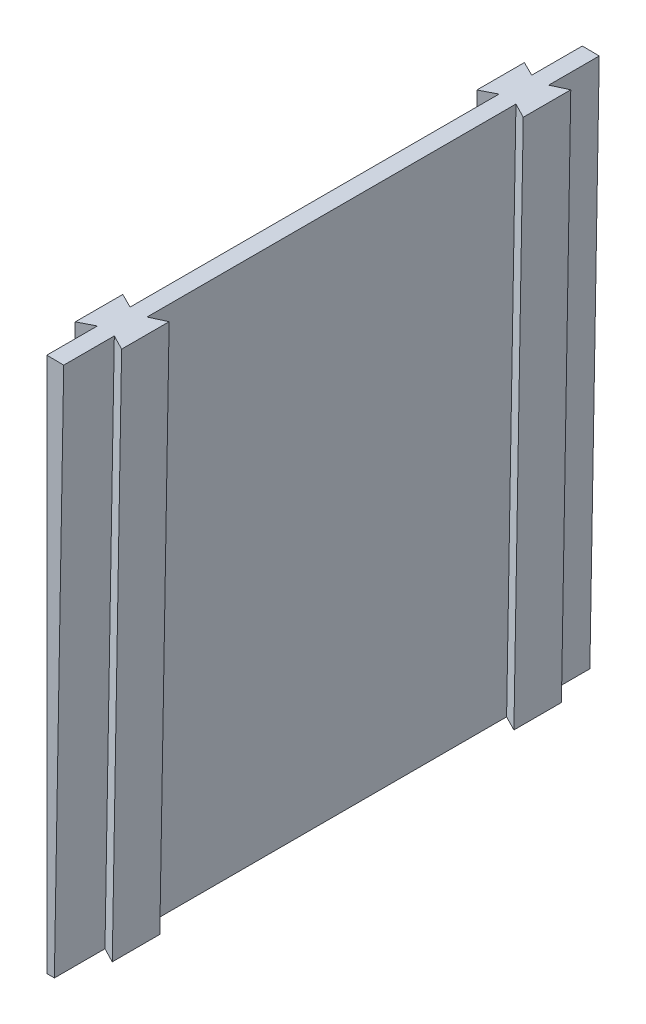
SolidWorks part; units mm, degrees
ref_plane "Front Plane" through (0, 0, 0) normal (0, 0, 1) x (1, 0, 0)
ref_plane "Top Plane" through (0, 0, 0) normal (0, 1, 0) x (1, 0, 0)
ref_plane "Right Plane" through (0, 0, 0) normal (1, 0, 0) x (0, 0, -1)
sketch "Sketch1" plane through (0, 0, 0) normal (0, 0, 1) x (1, 0, 0)
  line L0 (0, 82.55) -> (0, 184.15)
  line L1 (1.4407, 82.5374) -> (3.2139, 184.122)
  circle A0 centre (0, 0) radius 82.55 construction
  circle A1 centre (0, 0) radius 184.15 construction
  arc A2 (0, 184.15) -> (3.2139, 184.122) centre (0, 0) cw
  arc A3 (0, 82.55) -> (1.4407, 82.5374) centre (0, 0) cw
  dimension "D1" = 165.1
  dimension "D2" = 101.6
  dimension "D3" = 1
extrude "Boss-Extrude1" add sketch "Sketch1" along normal blind 101.6
ref_plane "Plane1" through (1.4407, 82.5374, 0) normal (-0.0175, -0.9998, 0) x (0, 0, -1)
sketch "Sketch2" plane through (1.4407, 82.5374, 0) normal (-0.0175, -0.9998, 0) x (0, 0, -1)
  line L10 (-92.0002, 0) -> (-93.4085, 2.794)
  line L15 (-101.6, 0) -> (0, 0) construction
  line L19 (-93.4085, 2.794) -> (-84.3915, 2.794)
  line L36 (-84.3915, 2.794) -> (-85.7998, 0)
  line L37 (-15.8002, 0) -> (-9.5998, 0)
  line L45 (-50.8, -1.4407) -> (-50.8, 25.7132) construction
  line L46 (-101.6, -1.4407) -> (0, -1.4407) construction
  line L55 (-85.7998, 0) -> (-92.0002, 0)
  line L56 (-17.2085, 2.794) -> (-15.8002, 0)
  line L57 (-8.1915, 2.794) -> (-17.2085, 2.794)
  line L58 (-9.5998, 0) -> (-8.1915, 2.794)
  point P4 (-88.9, 0)
  dimension "D1" = 63.25
  dimension "D2" = 9.017
  dimension "D3" = 2.794
  dimension "D4" = 12.7
extrude "Boss-Extrude2" add sketch "Sketch2" against normal up to surface (101.6 mm away)
ref_plane "Plane2" through (0, 82.55, 0) normal (0, -1, 0) x (0, 0, -1)
sketch "Sketch3" plane through (0, 82.55, 0) normal (0, -1, 0) x (0, 0, -1)
  line L0 (-92.0002, 0) -> (-93.4085, -2.7936)
  line L2 (-101.6, 0) -> (0, 0) construction
  line L13 (-93.4085, -2.7936) -> (-84.3915, -2.7936)
  line L14 (-84.3915, -2.7936) -> (-85.7998, 0)
  line L22 (-50.8, 0) -> (-50.8, 15.717) construction
  line L55 (-85.7998, 0) -> (-92.0002, 0)
  line L56 (-92.0002, 1.4407) -> (-85.7998, 1.4407) construction
  line L57 (-84.3915, 4.2343) -> (-93.4085, 4.2343) construction
  line L58 (-93.4085, 4.2343) -> (-92.0002, 1.4407) construction
  line L59 (-15.8002, 0) -> (-9.5998, 0)
  line L60 (-17.2085, -2.7936) -> (-15.8002, 0)
  line L61 (-8.1915, -2.7936) -> (-17.2085, -2.7936)
  line L62 (-9.5998, 0) -> (-8.1915, -2.7936)
  point P12 (-88.9, 1.4407)
  point P13 (-88.9, 0)
extrude "Boss-Extrude3" add sketch "Sketch3" against normal up to surface (101.5788 mm away)
